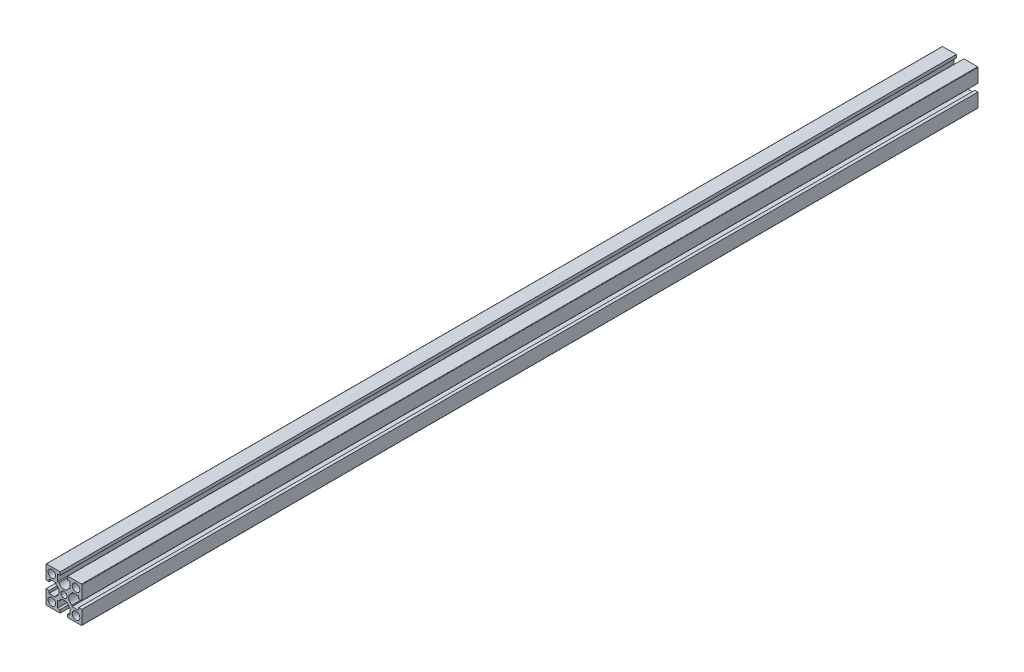
SolidWorks part; units mm, degrees
material "6063 T5"
ref_plane "Спереди" through (0, 0, 0) normal (0, 0, 1) x (1, 0, 0)
ref_plane "Сверху" through (0, 0, 0) normal (0, 1, 0) x (1, 0, 0)
ref_plane "Справа" through (0, 0, 0) normal (1, 0, 0) x (0, 0, -1)
sketch "Эскиз1" plane through (0, 0, 0) normal (0, 0, 1) x (1, 0, 0)
  line L0 (11.3549, 30.3863) -> (41.3549, 30.3863) construction
  line L10 (-20, 0) -> (20, 0) construction
  line L11 (-20, 7) -> (-20, 19.5)
  line L12 (-19.5, 20) -> (-3.4, 20)
  line L14 (7, 20) -> (19.5, 20)
  line L15 (20, 19.5) -> (20, 3.4)
  line L16 (20, -7) -> (20, -19.5)
  line L17 (19.5, -20) -> (3.4, -20)
  line L18 (-7, -20) -> (-19.5, -20)
  line L19 (-20, -19.5) -> (-20, -3.4)
  line L20 (-20.0402, 23.0813) -> (19.9598, 23.0813) construction
  line L21 (13.5, -13.5) -> (-13.5, -13.5) construction
  line L22 (13.5, -13.5) -> (13.5, 13.5) construction
  line L23 (13.5, 13.5) -> (-13.5, 13.5) construction
  line L24 (-13.5, -13.5) -> (-13.5, 13.5) construction
  line L25 (13.5, -13.5) -> (-13.5, 13.5) construction
  line L26 (13.5, 13.5) -> (-13.5, -13.5) construction
  circle A0 centre (-13.5, 13.5) radius 4.25
  circle A1 centre (13.5, 13.5) radius 4.25
  circle A2 centre (-13.5, -13.5) radius 4.25
  circle A3 centre (13.5, -13.5) radius 4.25
  circle A4 centre (0, 0) radius 3.4
  arc A5 (20, -19.5) -> (19.5, -20) centre (19.5, -19.5) cw
  arc A6 (-19.5, -20) -> (-20, -19.5) centre (-19.5, -19.5) cw
  arc A7 (19.5, 20) -> (20, 19.5) centre (19.5, 19.5) cw
  arc A8 (-20, 19.5) -> (-19.5, 20) centre (-19.5, 19.5) cw
  point P4 (0, 0)
  point P17 (0, 0)
  line B0 (-20, 7) -> (-20, 4.2)
  line B1 (-20, 4.2) -> (-16.5, 4.2)
  line B2 (-16.5, 4.2) -> (-16.5, 7)
  line B3 (-16.5, 7) -> (-9, 7)
  line B4 (-9, -7) -> (-16.5, -7)
  line B5 (-16.5, -7) -> (-16.5, -4.2)
  line B6 (-16.5, -4.2) -> (-20, -4.2)
  line B7 (-20, -4.2) -> (-20, -7)
  line B8 (-20, 7) -> (-20, -7) construction
  line B9 (-9, 7) -> (-9, 5.5417)
  line B10 (-9, -7) -> (-9, -5.5417)
  arc B11 (-9, 5.5417) -> (-9, -5.5417) centre (-11.3, 0) cw
  line B12 (7, 20) -> (4.2, 20)
  line B13 (4.2, 20) -> (4.2, 16.5)
  line B14 (4.2, 16.5) -> (7, 16.5)
  line B15 (7, 16.5) -> (7, 9)
  line B16 (-7, 9) -> (-7, 16.5)
  line B17 (-7, 16.5) -> (-4.2, 16.5)
  line B18 (-4.2, 16.5) -> (-4.2, 20)
  line B19 (-4.2, 20) -> (-7, 20)
  line B20 (7, 20) -> (-7, 20) construction
  line B21 (7, 9) -> (5.5417, 9)
  line B22 (-7, 9) -> (-5.5417, 9)
  arc B23 (5.5417, 9) -> (-5.5417, 9) centre (0, 11.3) cw
  line B24 (20, -7) -> (20, -4.2)
  line B25 (20, -4.2) -> (16.5, -4.2)
  line B26 (16.5, -4.2) -> (16.5, -7)
  line B27 (16.5, -7) -> (9, -7)
  line B28 (9, 7) -> (16.5, 7)
  line B29 (16.5, 7) -> (16.5, 4.2)
  line B30 (16.5, 4.2) -> (20, 4.2)
  line B31 (20, 4.2) -> (20, 7)
  line B32 (20, -7) -> (20, 7) construction
  line B33 (9, -7) -> (9, -5.5417)
  line B34 (9, 7) -> (9, 5.5417)
  arc B35 (9, -5.5417) -> (9, 5.5417) centre (11.3, 0) cw
  line B36 (-7, -20) -> (-4.2, -20)
  line B37 (-4.2, -20) -> (-4.2, -16.5)
  line B38 (-4.2, -16.5) -> (-7, -16.5)
  line B39 (-7, -16.5) -> (-7, -9)
  line B40 (7, -9) -> (7, -16.5)
  line B41 (7, -16.5) -> (4.2, -16.5)
  line B42 (4.2, -16.5) -> (4.2, -20)
  line B43 (4.2, -20) -> (7, -20)
  line B44 (-7, -20) -> (7, -20) construction
  line B45 (-7, -9) -> (-5.5417, -9)
  line B46 (7, -9) -> (5.5417, -9)
  arc B47 (-5.5417, -9) -> (5.5417, -9) centre (0, -11.3) cw
  dimension "D5" = 8.5
  dimension "D6" = 6.8
  dimension "D8" = 0.5
  dimension "D1" = 30
  dimension "D2" = 40
  dimension "D3" = 4
  dimension "D4" = 27
  dimension "D7" = 40
sketch_block_instance "Блок1-1"
sketch_block "Блок1" parameters "D4"=6.5, "D1"=14, "D2"=8.4, "D3"=2.2, "D5"=6, "D6"=1.3698
sketch_block_instance "Блок1-2"
sketch_block_instance "Блок1-3"
sketch_block_instance "Блок1-4"
extrude "Бобышка-Вытянуть1" add sketch "Эскиз1" along normal blind 1000
